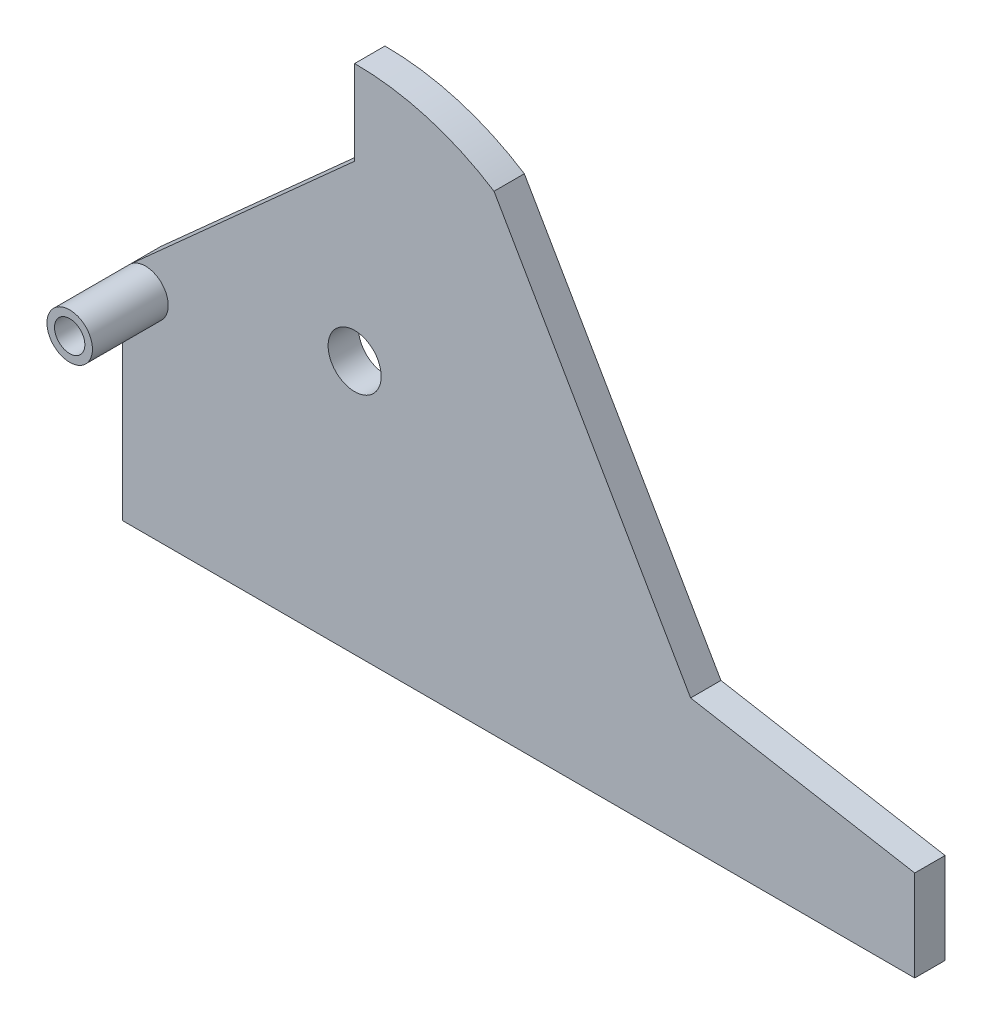
SolidWorks part; units mm, degrees
ref_plane "Front Plane" through (0, 0, 0) normal (0, 0, 1) x (1, 0, 0)
ref_plane "Top Plane" through (0, 0, 0) normal (0, 1, 0) x (1, 0, 0)
ref_plane "Right Plane" through (0, 0, 0) normal (1, 0, 0) x (0, 0, -1)
sketch "Sketch1" plane through (0, 0, 0) normal (0, 0, 1) x (1, 0, 0)
  line L0 (-54.9958, 0) -> (67.63, 0) construction
  line L1 (0, 23.262) -> (0, -27.492) construction
  line L2 (0, 0) -> (522.5, 0)
  line L3 (0, 0) -> (0, 138)
  line L8 (4.9848, 149.1667) -> (129.7305, 261.0488)
  line L10 (129.7305, 261.0488) -> (153, 281.9188)
  line L11 (153, 281.9188) -> (153, 337.7402)
  line L13 (244.94, 310.7333) -> (374.6494, 86.07)
  line L14 (522.5, 0) -> (522.5, 60)
  line L15 (522.5, 60) -> (374.6494, 86.07)
  circle A0 centre (15, 138) radius 15
  circle A2 centre (15, 138) radius 10
  arc A4 (244.94, 310.7333) -> (153, 337.7402) centre (153, 167.7402) ccw
  circle A5 centre (153, 167.7402) radius 17.5
  point P15 (153, 167.7402)
  dimension "D3" = 30
  dimension "D2" = 170
extrude "Boss-Extrude1" add sketch "Sketch1" along normal blind 20 contours L13 A4 L11 L10 L8 A0 L3 L2 L14 L15 A5 | A2
sketch "Sketch2" plane through (0, 0, 20) normal (0, 0, 1) x (1, 0, 0)
  circle A0 centre (15, 138) radius 10
  circle A1 centre (15, 138) radius 15
extrude "Boss-Extrude2" add sketch "Sketch2" along normal blind 50
sketch "Sketch3" plane through (0, 0, 0) normal (0, 0, -1) x (-1, 0, 0)
  circle A0 centre (-15, 138) radius 24.4466
  circle A1 centre (-153, 167.7402) radius 60.5372
